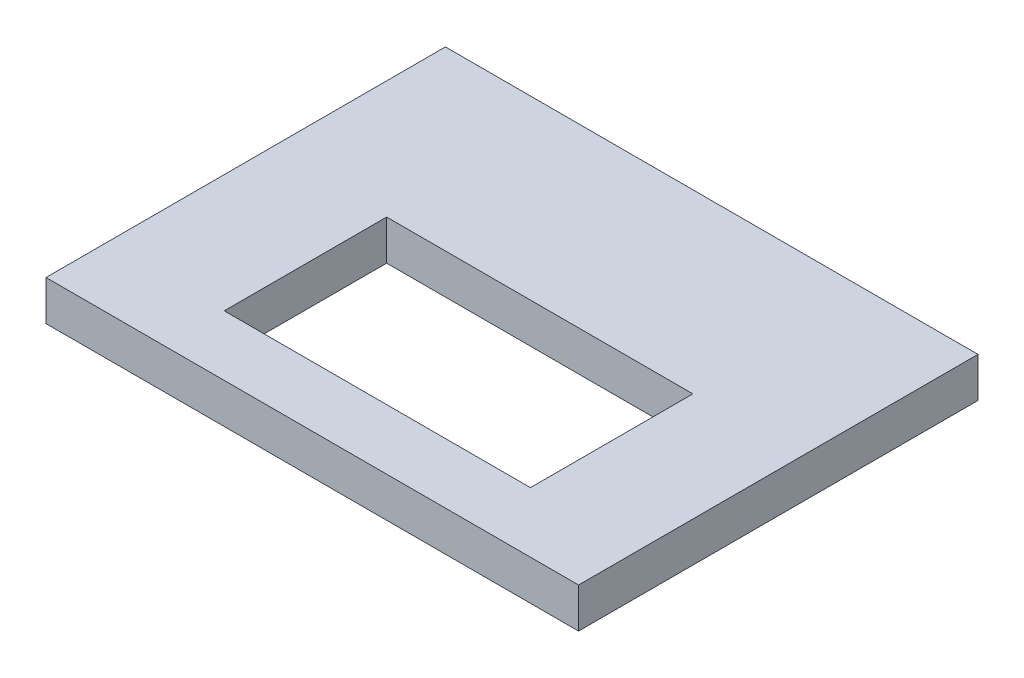
SolidWorks part; units mm, degrees
ref_plane "Front Plane" through (0, 0, 0) normal (0, 0, 1) x (1, 0, 0)
ref_plane "Top Plane" through (0, 0, 0) normal (0, 1, 0) x (1, 0, 0)
ref_plane "Right Plane" through (0, 0, 0) normal (1, 0, 0) x (0, 0, -1)
sketch "Sketch1" plane through (0, 0, 0) normal (0, 1, 0) x (1, 0, 0)
  line L1 (-55.8758, 14.3684) -> (-15.8758, 14.3684)
  line L2 (-55.8758, 14.3684) -> (-55.8758, -15.6316)
  line L3 (-55.8758, -15.6316) -> (-15.8758, -15.6316)
  line L4 (-15.8758, 14.3684) -> (-15.8758, -15.6316)
  line L5 (-47.015, 1.0932) -> (-24.015, 1.0932)
  line L6 (-47.015, 1.0932) -> (-47.015, -11.1068)
  line L7 (-47.015, -11.1068) -> (-24.015, -11.1068)
  line L8 (-24.015, 1.0932) -> (-24.015, -11.1068)
  dimension "D1" = 40
  dimension "D2" = 30
  dimension "D3" = 23
  dimension "D4" = 12.2
extrude "Boss-Extrude1" add sketch "Sketch1" along normal blind 3
